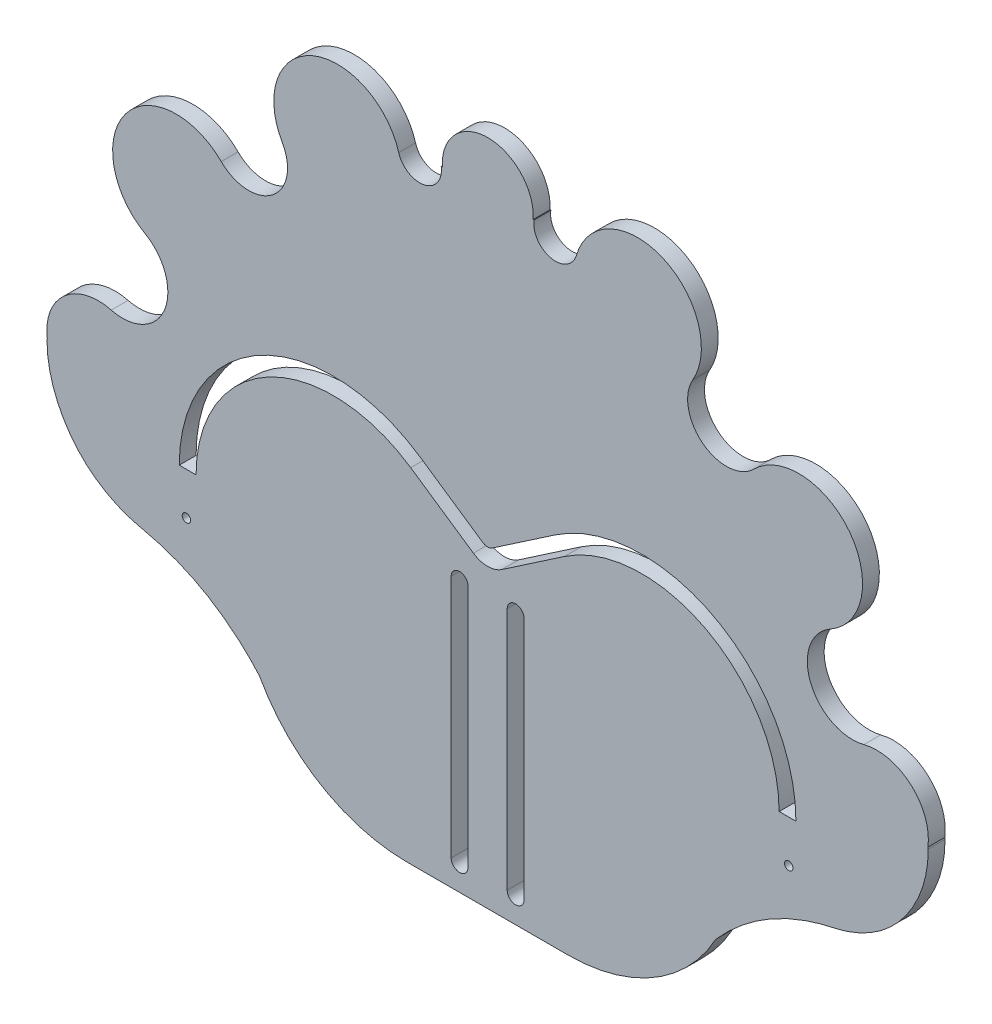
SolidWorks part; units mm, degrees
ref_plane "Front Plane" through (0, 0, 0) normal (0, 0, 1) x (1, 0, 0)
ref_plane "Top Plane" through (0, 0, 0) normal (0, 1, 0) x (1, 0, 0)
ref_plane "Right Plane" through (0, 0, 0) normal (1, 0, 0) x (0, 0, -1)
sketch "Sketch2" plane through (0, 0, 0) normal (0, 0, 1) x (1, 0, 0)
  line L0 (0, 0) -> (0, 90.61) construction
  line L1 (-149.6592, 0) -> (149.6592, 0) construction
  line L2 (0, 0) -> (89.5664, 89.5664)
  line L3 (0, 0) -> (31.3254, 116.9082)
  line L4 (0, 0) -> (-137.9751, 36.9703)
  line L5 (0, 0) -> (114.8367, 66.301)
  line L6 (0, 0) -> (-114.8367, 66.301)
  line L7 (0, 0) -> (59.8625, 103.6849)
  line L8 (0, 0) -> (-89.5664, 89.5664)
  line L9 (0, 0) -> (137.9751, 36.9703)
  line L10 (0, 0) -> (-59.8625, 103.6849)
  line L11 (0, 0) -> (-31.3254, 116.9082)
  line L12 (-234.2065, 0) -> (234.2065, 0)
  arc A0 (70, 0) -> (-70, 0.0721) centre (0, 0) ccw
  circle A2 centre (-69.4205, 8.9889) radius 9.1985
  circle A3 centre (-65.1052, 25.716) radius 8.0763
  circle A4 centre (-55.5306, 42.6186) radius 11.3498
  circle A5 centre (-42.6072, 55.5394) radius 6.9249
  circle A6 centre (-26.7646, 64.6812) radius 11.3661
  circle A7 centre (-12.1201, 68.9427) radius 3.8858
  circle A8 centre (69.4205, 8.9889) radius 9.1985
  circle A9 centre (65.1052, 25.716) radius 8.0763
  circle A10 centre (55.5306, 42.6186) radius 11.3498
  circle A11 centre (42.6072, 55.5394) radius 6.9249
  circle A12 centre (26.7646, 64.6812) radius 11.3661
  circle A13 centre (12.1201, 68.9427) radius 3.8858
  circle A14 centre (0.036, 70) radius 8.1218
  point P9 (0, 0)
  point P57 (0, 0)
  dimension "D1" = 70
  dimension "D2" = 15
  dimension "D3" = 15
  dimension "D4" = 15
  dimension "D5" = 15
  dimension "D6" = 15
extrude "Boss-Extrude3" add sketch "Sketch2" along normal blind 3
sketch "Sketch4" plane through (0, 0, 0) normal (0, 0, 1) x (1, 0, 0)
  line L0 (0, 99.896) -> (0, -99.896) construction
  line L1 (-78.5829, 29.1229) -> (-78.5829, 7.5) construction
  line L2 (0.0402, 78.1218) -> (8.5761, 78.1218) construction
  line L3 (0.0402, 78.1218) -> (-8.3939, 78.1218) construction
  line L4 (-91.7707, 0) -> (91.7707, 0) construction
  line L5 (-58.163, -13.5) -> (-57.5829, -13.5) construction
  line L6 (-71.373, 26.7531) -> (-71.373, -26.7531) construction
  line L7 (71.373, 25.5873) -> (71.373, -25.5873) construction
  line L8 (-44.373, 0) -> (-44.373, -46.131) construction
  line L9 (44.373, 0) -> (44.373, -41.8644) construction
  line L10 (-57.873, 0) -> (-57.873, -21.1924)
  line L11 (57.873, 0) -> (57.873, -16.871)
  line L12 (0.0402, 78.1218) -> (0, 0)
  line L13 (0, 0) -> (-57.873, 0)
  line L14 (0, 0) -> (57.873, 0)
  line L15 (-42.873, 0) -> (-44.373, 0)
  line L16 (-44.373, 0) -> (42.873, 0)
  line L17 (44.373, 0) -> (42.873, 0)
  line L18 (-9.077, 32.1518) -> (9.0873, 32.1518) construction
  line L19 (-38.522, 13.3276) -> (-25.4708, 25.6058) construction
  line L20 (25.0327, 26.4266) -> (38.8336, 12.6256) construction
  line L21 (-42.873, 0) -> (-44.373, 0)
  line L22 (42.873, 0) -> (44.373, 0)
  line L23 (-78.5829, 7.5) -> (-78.5363, 7.759)
  line L24 (-78.5363, 7.759) -> (-77.9561, 5.5604)
  line L25 (-77.9561, 5.5604) -> (-76.892, 3.6235)
  line L26 (-76.892, 3.6235) -> (-75.393, 1.9931)
  line L27 (-75.393, 1.9931) -> (-73.4845, 0.7369)
  line L28 (-73.4845, 0.7369) -> (-71.373, 0)
  line L29 (78.5829, 7.5) -> (78.5363, 7.759)
  line L30 (78.5363, 7.759) -> (77.9561, 5.5604)
  line L31 (77.9561, 5.5604) -> (76.892, 3.6235)
  line L32 (76.892, 3.6235) -> (75.393, 1.9931)
  line L33 (75.393, 1.9931) -> (73.4845, 0.7369)
  line L34 (73.4845, 0.7369) -> (71.373, 0)
  arc A0 (8.1439, 69.5247) -> (-8.0723, 69.533) centre (0.036, 70) ccw construction
  circle A1 centre (0, -14.5438) radius 46.6957
  arc A2 (-78.5829, 7.5) -> (-57.5829, -13.5) centre (-57.5829, 7.5) ccw construction
  circle A5 centre (57.873, 0) radius 13.5
  circle A6 centre (-57.873, 0) radius 13.5
  arc A7 (78.5829, 7.5) -> (57.5829, -13.5) centre (57.5829, 7.5) cw construction
  arc A8 (-67.1227, 17.8957) -> (-71.373, 0) centre (-69.4205, 8.9889) ccw construction
  arc A9 (71.373, 0) -> (67.1227, 17.8957) centre (69.4205, 8.9889) ccw construction
  spline S0 degree 3 poles (-42.873, 0) (-37.4459, 17.8901) (0.0146, 43.4121) (37.4522, 17.8932) (42.873, 0) knots 0 0 0 0 0.500092 1 1 1 1
  spline S1 degree 3 poles (-78.5829, 7.5) (-78.6194, 2.111) (-75.054, -6.4031) (-65.6924, -12.4338) (-60.1889, -13.5421) (-57.5829, -13.5) knots 0 0 0 0 0.497531 0.760342 1 1 1 1
  spline S2 degree 3 poles (78.5829, 7.5) (78.6747, 1.5357) (73.5011, -9.4072) (62.638, -13.5146) (57.5829, -13.5) knots 0 0 0 0 0.543339 1 1 1 1
  point P4 (0, 0)
  point P14 (0, 0)
  point P18 (-71.373, 0)
  point P23 (71.373, 0)
  point P36 (-78.5829, 18.3115)
  point P39 (-57.873, -13.5)
  point P52 (0.0052, 32.1518)
  point P55 (-31.9964, 19.4667)
  point P58 (31.9331, 19.5261)
  dimension "D5" = 21
  dimension "D6" = 1.5
  dimension "D1" = 27
  dimension "D2" = 27
  dimension "D3" = 13.5
  dimension "D4" = 13.5
  dimension "D7" = 1.5
  dimension "D8" = 1.5
  dimension "D9" = 1.5
  dimension "D10" = 1.5
extrude "Boss-Extrude4" add sketch "Sketch4" along normal blind 3 contours L13 S0 L12 A1 | L12 S0 L14 A1 | L23 S1 L10 A6 L28 L27 L26 L25 L24 | L13 A6 L10 | L10 A6 A1 L13 | S2 L11 L14 A1 A5 | S2 A5 L14 L11 | S2 L29 L30 L31 L32 L33 L34 A5
sketch "Sketch5" plane through (0, 0, 0) normal (0, 0, 1) x (1, 0, 0)
  line L0 (-77.198, 0) -> (77.198, 0) construction
  line L1 (-55, 0) -> (-53.5, 0)
  line L2 (0, 78.1218) -> (0, -78.1218) construction
  line L3 (48.8784, 0) -> (55, 0)
  line L4 (-55, 0) -> (-52, 0)
  line L5 (51.9392, 0) -> (55, 0)
  line L6 (-12.0274, 22.7343) -> (-0.844, 15.123)
  line L7 (12.0274, 22.7343) -> (0.844, 15.123)
  line L8 (-2.5319, 12.6429) -> (-13.7153, 20.2542)
  line L9 (2.5319, 12.6429) -> (13.7153, 20.2542)
  circle A0 centre (0, 16.3631) radius 4.5
  circle A1 centre (27.5, 0) radius 27.5
  circle A2 centre (-27.5, 0) radius 27.5
  circle A5 centre (0, 16.3631) radius 1.5
  circle A6 centre (27.5, 0) radius 24.5
  circle A7 centre (-27.5, 0) radius 24.5
  spline S0 degree 3 poles (78.5829, 7.5) (78.6747, 1.5357) (73.531, -9.3439) (62.7635, -13.4668) (57.775, -13.4996) knots 0 0 0 0 0.543339 0.994213 0.994213 0.994213 0.994213 construction
  point P4 (0, 0)
  point P8 (0, 0)
  dimension "D1" = 3
  dimension "D2" = 16.3631
  dimension "D3" = 3
  dimension "D4" = 9
extrude "Cut-Extrude11" cut sketch "Sketch5" along normal through all both and the other way through all contours L4 A7 L8 A2 L1 | A5 L6 A0 L7 | A6 L5 A1 L9 | L6 A2 A0 | A1 L7 A0 | A0 A2 L8 | A1 A0 L9
sketch "Sketch6" plane through (0, 0, 0) normal (0, 0, 1) x (1, 0, 0)
  line L0 (0, -89.1359) -> (0, 89.1359) construction
  line L1 (-44.373, 0) -> (44.373, 0) construction
  line L2 (-15, 0) -> (15, 0)
  line L3 (-15, 0) -> (-15, -41)
  line L4 (-15, -41) -> (15, -41)
  line L5 (15, 0) -> (15, -41)
  point P4 (0, 0)
  dimension "D1" = 41
  dimension "D2" = 30
  dimension "D3" = 15
extrude "Boss-Extrude5" add sketch "Sketch6" along normal blind 40
sketch "Sketch7" plane through (0, 0, 0) normal (0, 1, 0) x (1, 0, 0)
  line L1 (-44.373, -3) -> (44.373, -3)
  line L2 (-44.373, -3) -> (-44.373, 0)
  line L3 (-44.373, 0) -> (44.373, 0)
  line L4 (44.373, -3) -> (44.373, 0)
extrude "Boss-Extrude6" add sketch "Sketch7" against normal blind 41
sketch "Sketch8" plane through (0, 0, 0) normal (0, 0, 1) x (1, 0, 0)
  line L0 (44.373, 0) -> (44.373, -41)
  line L1 (44.373, -41) -> (-14.373, -41)
  line L2 (-44.373, -11) -> (-44.373, 0)
  line L3 (0, 0) -> (0, -48.4098) construction
  line L4 (44.373, 0) -> (44.373, -46.5184)
  line L5 (44.373, -46.5184) -> (-44.373, -46.5184)
  line L6 (-44.373, -46.5184) -> (-44.373, -11)
  arc A0 (-44.373, -11) -> (-14.373, -41) centre (-14.373, -11) ccw
  arc A1 (44.373, -11) -> (14.373, -41) centre (14.373, -11) cw
  point P13 (-44.373, -41)
  dimension "D1" = 30
extrude "Cut-Extrude12" cut sketch "Sketch8" against normal through all and the other way through all contours L4 A1 L1 | L3 L1 A0 L6 L5 | L1 L3 L5 L4
sketch "Sketch10" plane through (0, 0, 0) normal (0, 0, 1) x (1, 0, 0)
  line L0 (0, 48.3616) -> (0, -48.3616) construction
  line L1 (-62.1374, -13.0143) -> (-43.0357, 6.0874)
  line L2 (-43.0357, 6.0874) -> (-28.6321, -11.4184)
  line L3 (-28.6321, -11.4184) -> (-35.8067, -31.9903)
  line L4 (43.0357, 6.0874) -> (28.6321, -11.4184)
  line L5 (62.1374, -13.0143) -> (43.0357, 6.0874)
  line L6 (28.6321, -11.4184) -> (35.8067, -31.9903)
  arc A0 (-44.373, -11) -> (-15, -40.9934) centre (-14.373, -11) ccw construction
  spline S0 degree 2 poles (-62.1374, -13.0143) (-45.4935, -16.3889) (-35.8067, -31.9903) knots 0 0 0 1 1 1
  spline S1 degree 3 poles (-78.5829, 7.5) (-78.6194, 2.111) (-75.054, -6.4031) (-65.7756, -12.3802) (-60.3834, -13.5023) (-57.873, -13.5023) knots 0 0 0 0 0.497531 0.760342 0.991111 0.991111 0.991111 0.991111 construction
  spline S2 degree 2 poles (62.1374, -13.0143) (45.4935, -16.3889) (35.8067, -31.9903) knots 0 0 0 1 1 1
  point P12 (0, 0)
extrude "Boss-Extrude7" add sketch "Sketch10" along normal blind 3
sketch "Sketch11" plane through (0, 0, 0) normal (0, 0, 1) x (1, 0, 0)
  line L0 (-15, 0) -> (15, 0)
  line L1 (15, 0) -> (15, -13.6)
  line L2 (15, -40.9934) -> (15, 0) construction
  line L3 (15, -13.6) -> (5, -13.6)
  line L4 (5, -13.6) -> (5, -27.3934)
  line L5 (5, -27.3934) -> (15, -27.3934)
  line L6 (15, -40.9934) -> (15, 0) construction
  line L7 (15, -27.3934) -> (15, -40.9934)
  line L8 (15, -40.9934) -> (-14.373, -41)
  line L9 (0, 50.8169) -> (0, -50.8169) construction
  line L10 (-15, -40.9934) -> (14.373, -41)
  line L11 (-15, -27.3934) -> (-15, -40.9934)
  line L12 (-5, -27.3934) -> (-15, -27.3934)
  line L13 (-5, -13.6) -> (-5, -27.3934)
  line L14 (-15, -13.6) -> (-5, -13.6)
  line L15 (-15, 0) -> (-15, -13.6)
  line L16 (-15, -13.6) -> (-15, -27.3934)
  line L17 (15, -13.6) -> (15, -27.3934)
  point P20 (0, 0)
  point P26 (5, -20.4967)
  dimension "D1" = 13.6
  dimension "D2" = 13.6
  dimension "D3" = 10
extrude "Cut-Extrude13" cut sketch "Sketch11" along normal blind 41 from offset 3 contours L14 L16 L12 L13 | L17 L3 L4 L5
sketch "Sketch12" plane through (0, 0, 0) normal (0, 1, 0) x (1, 0, 0)
  line L0 (0, 58.0711) -> (0, -58.0711) construction
  line L5 (-15, -3) -> (15, -3) construction
  circle A2 centre (0, -24) radius 1.55
  point P4 (0, 0)
  dimension "D1" = 3.1
  dimension "D2" = 21
extrude "Cut-Extrude14" cut sketch "Sketch12" against normal through all and the other way through all
sketch "Sketch13" plane through (0, 0, 0) normal (0, 0, 1) x (1, 0, 0)
  line L0 (0, -81.405) -> (0, 81.405) construction
  circle A0 centre (-53.715, -7.516) radius 0.75
  circle A1 centre (53.715, -7.516) radius 0.75
  point P4 (0, 0)
  dimension "D1" = 1.5
extrude "Cut-Extrude15" cut sketch "Sketch13" against normal through all both and the other way through all
sketch "Sketch14" plane through (0, 0, 0) normal (0, 0, 1) x (1, 0, 0)
  line L1 (-15, 0) -> (15.4163, 0)
  line L2 (-15, 0) -> (-15, -42.9077)
  line L3 (-15, -42.9077) -> (15.4163, -42.9077)
  line L4 (15.4163, 0) -> (15.4163, -42.9077)
extrude "Cut-Extrude17" cut sketch "Sketch14" along normal blind 41 from offset 3
sketch "Sketch16" plane through (0, 0, 0) normal (0, 0, 1) x (1, 0, 0)
  line L0 (0, -67.4778) -> (0, 67.4778) construction
  line L1 (-14.373, -41) -> (14.373, -41) construction
  line L2 (-10, 10) -> (10, 10)
  line L3 (-10, 10) -> (-10, -40)
  line L4 (-10, -40) -> (10, -40)
  line L5 (10, 10) -> (10, -40)
  line L6 (-10, 10) -> (10, -40) construction
  line L7 (-10, -40) -> (10, 10) construction
  line L8 (-5, -51.3222) -> (-5, 21.3222) construction
  line L9 (-6.5, 7.0855) -> (-6.5, -34.0746)
  line L10 (-3.5, 7.0855) -> (-3.5, -34.0746)
  line L11 (3.5, 7.0855) -> (3.5, -34.0746)
  line L12 (6.5, 7.0855) -> (6.5, -34.0746)
  line L13 (-6.5, -34.0746) -> (-6.5, -36.4145)
  line L14 (-3.5, -34.0746) -> (-3.5, -36.4145)
  line L15 (3.5, -34.0746) -> (3.5, -36.4145)
  line L16 (6.5, -34.0746) -> (6.5, -36.4145)
  circle A0 centre (-5, 7.0855) radius 1.5
  circle A3 centre (-5, -36.4145) radius 1.5
  circle A5 centre (5, -36.4145) radius 1.5
  circle A6 centre (5, 7.0855) radius 1.5
  point P0 (0, -15)
  point P4 (0, 0)
  point P14 (-5, -15)
  dimension "D5" = 3
  dimension "D6" = 45
  dimension "D8" = 3
  dimension "D1" = 50
  dimension "D2" = 20
  dimension "D3" = 1
  dimension "D4" = 5
extrude "Cut-Extrude19" cut sketch "Sketch16" against normal through all both and the other way through all contours A0 | A6 | L12 A6 L11 L15 A5 L16 | A3 L14 L10 A0 L9 L13 | A3 | A5
